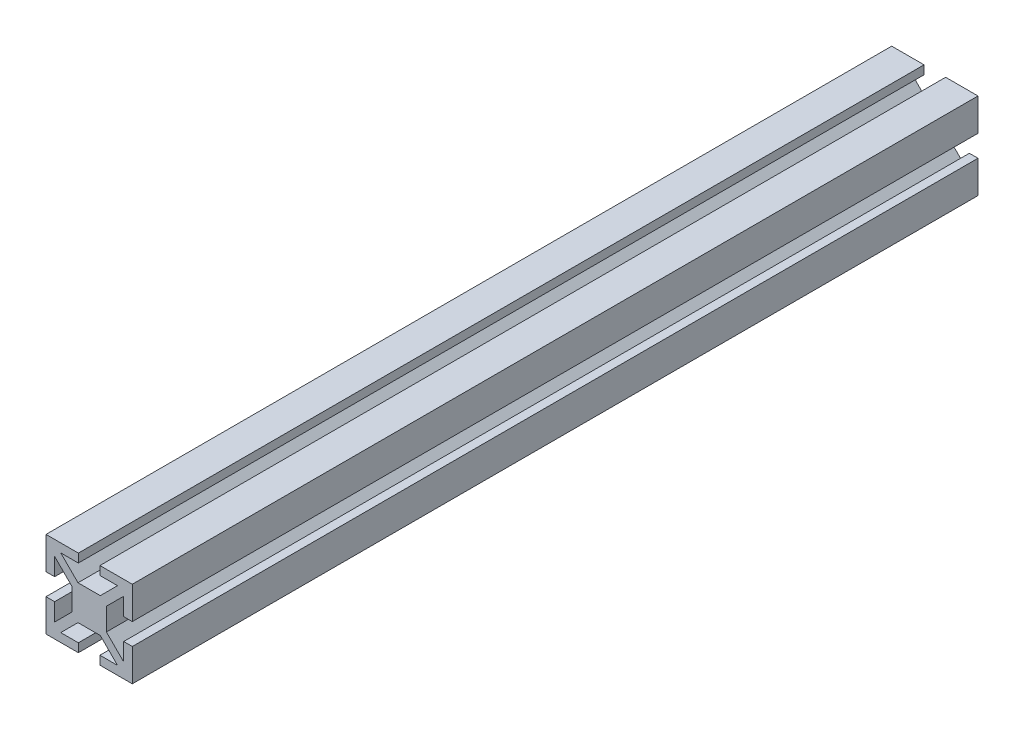
SolidWorks part; units mm, degrees
ref_plane "Front Plane" through (0, 0, 0) normal (0, 0, 1) x (1, 0, 0)
ref_plane "Top Plane" through (0, 0, 0) normal (0, 1, 0) x (1, 0, 0)
ref_plane "Right Plane" through (0, 0, 0) normal (1, 0, 0) x (0, 0, -1)
sketch "Sketch1" plane through (0, 0, 0) normal (0, 0, 1) x (1, 0, 0)
  line L0 (0, 4) -> (0, -4) construction
  line L1 (-2.5858, 4) -> (2.5858, 4)
  line L2 (-4, 2.5858) -> (-4, -2.5858)
  line L5 (-10, 10) -> (0, 0) construction
  line L6 (0, 10) -> (0, 4) construction
  line L7 (-4, 2.5858) -> (-8, 6.5858)
  line L8 (-6.5858, 8) -> (-2.5, 8)
  line L9 (-2.5, 8) -> (-2.5, 10)
  line L10 (-2.5, 10) -> (-10, 10)
  line L11 (-10, 10) -> (-10, 2.5)
  line L12 (-10, 2.5) -> (-8, 2.5)
  line L13 (-8, 2.5) -> (-8, 6.5858)
  line L14 (-4, 0) -> (4, 0) construction
  line L15 (-4, 0) -> (-10, 0) construction
  line L16 (-2.5858, 4) -> (-6.5858, 8)
  line L17 (-10, -10) -> (0, 0) construction
  line L18 (-2.5858, -4) -> (-6.5858, -8)
  line L19 (-8, -2.5) -> (-8, -6.5858)
  line L20 (-10, -2.5) -> (-8, -2.5)
  line L21 (-10, -10) -> (-10, -2.5)
  line L22 (-2.5, -10) -> (-10, -10)
  line L23 (-2.5, -8) -> (-2.5, -10)
  line L24 (-6.5858, -8) -> (-2.5, -8)
  line L25 (-4, -2.5858) -> (-8, -6.5858)
  line L26 (-2.5858, -4) -> (2.5858, -4)
  line L27 (10, -10) -> (0, 0) construction
  line L28 (4, 0) -> (10, 0) construction
  line L29 (10, 10) -> (0, 0) construction
  line L30 (4, -2.5858) -> (8, -6.5858)
  line L31 (6.5858, -8) -> (2.5, -8)
  line L32 (2.5, -8) -> (2.5, -10)
  line L33 (2.5, -10) -> (10, -10)
  line L34 (10, -10) -> (10, -2.5)
  line L35 (10, -2.5) -> (8, -2.5)
  line L36 (8, -2.5) -> (8, -6.5858)
  line L37 (2.5858, -4) -> (6.5858, -8)
  line L38 (2.5858, 4) -> (6.5858, 8)
  line L39 (8, 2.5) -> (8, 6.5858)
  line L40 (10, 2.5) -> (8, 2.5)
  line L41 (10, 10) -> (10, 2.5)
  line L42 (2.5, 10) -> (10, 10)
  line L43 (2.5, 8) -> (2.5, 10)
  line L44 (6.5858, 8) -> (2.5, 8)
  line L45 (4, 2.5858) -> (8, 6.5858)
  line L46 (4, 2.5858) -> (4, -2.5858)
  point P0 (0, 0)
  dimension "D1" = 10
  dimension "D2" = 4
  dimension "D3" = 2
  dimension "D4" = 10
  dimension "D5" = 2
  dimension "D6" = 2.5
  dimension "D7" = 2.5
  dimension "D8" = 4
  dimension "D9" = 1
  dimension "D10" = 1
extrude "Boss-Extrude1" add sketch "Sketch1" along normal mid plane 196
sketch "Sketch2" plane through (4, 0, 0) normal (1, 0, 0) x (0, 0, -1)
  line L1 (98, -2.5858) -> (98, 2.5858) construction
  circle A0 centre (88, 0) radius 2.5
  dimension "D1" = 5
  dimension "D2" = 10
extrude "Cut-Extrude1" cut sketch "Sketch2" against normal blind 10
